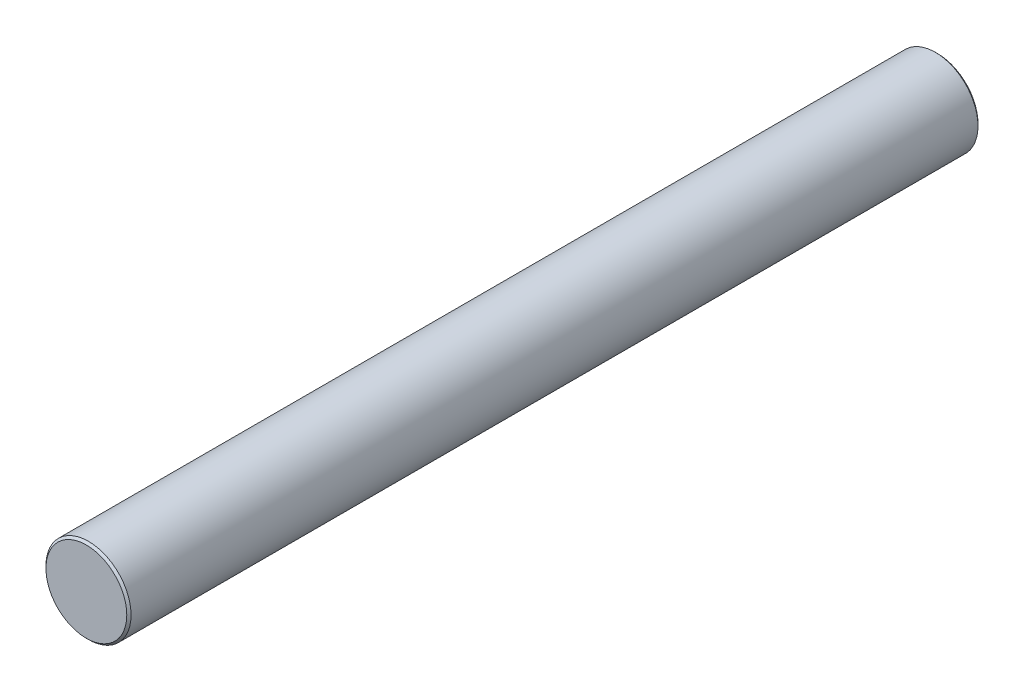
SolidWorks part; units mm, degrees
ref_plane "Front Plane" through (0, 0, 0) normal (0, 0, 1) x (1, 0, 0)
ref_plane "Top Plane" through (0, 0, 0) normal (0, 1, 0) x (1, 0, 0)
ref_plane "Right Plane" through (0, 0, 0) normal (1, 0, 0) x (0, 0, -1)
sketch "Sketch1" plane through (0, 0, 0) normal (0, 0, 1) x (1, 0, 0)
  circle A0 centre (0, 0) radius 5.08
  dimension "D1" = 10.16
extrude "Boss-Extrude1" add sketch "Sketch1" along normal mid plane 101.6
chamfer "Chamfer1" distance 0.254 angle 45 2 edges at (5.08, 0, 50.8) (5.08, 0, -50.8)
